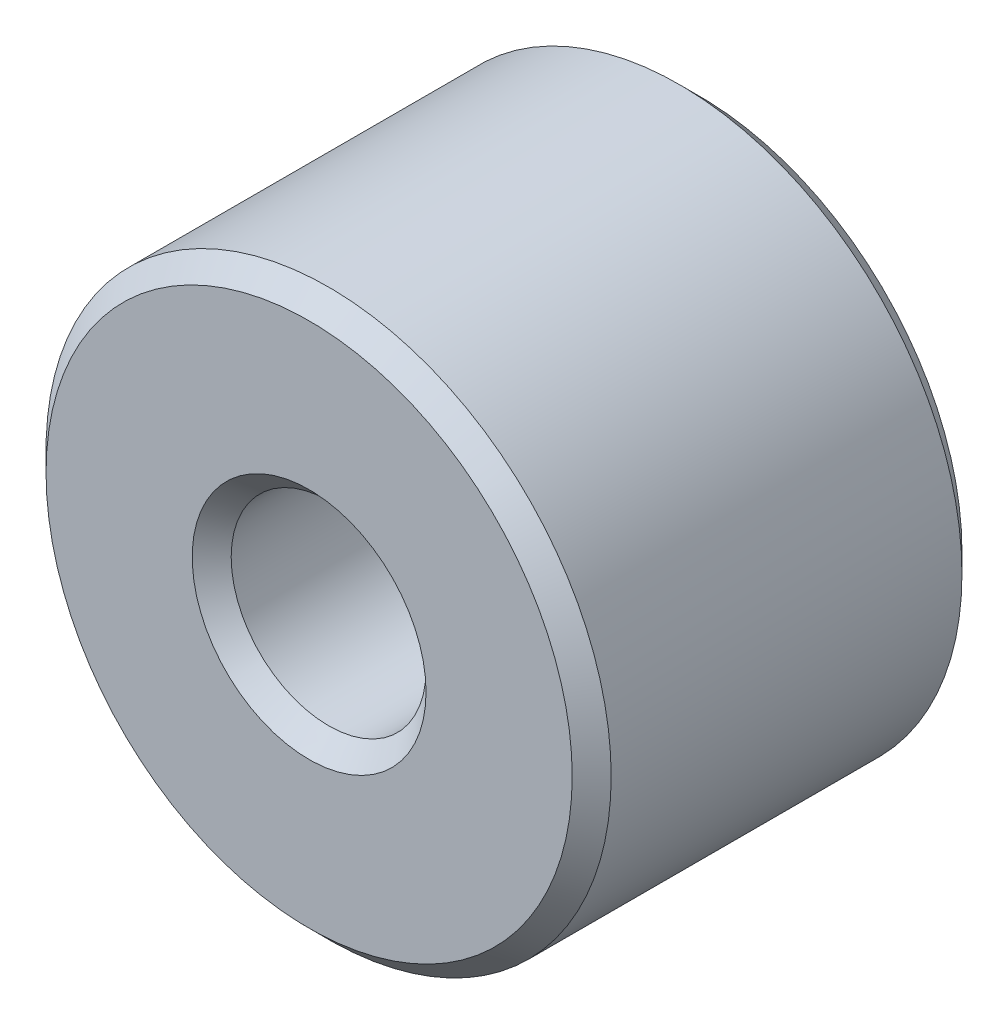
SolidWorks part; units mm, degrees
material "Plain Carbon Steel"
ref_plane "Front Plane" through (0, 0, 0) normal (0, 0, 1) x (1, 0, 0)
ref_plane "Top Plane" through (0, 0, 0) normal (0, 1, 0) x (1, 0, 0)
ref_plane "Right Plane" through (0, 0, 0) normal (1, 0, 0) x (0, 0, -1)
sketch "Sketch1" plane through (0, 0, 0) normal (0, 0, 1) x (1, 0, 0)
  circle A0 centre (0, 0) radius 7.25
  circle A1 centre (0, 0) radius 2.5
  dimension "D1" = 5
  dimension "D2" = 14.5
extrude "Boss-Extrude1" add sketch "Sketch1" along normal blind 10
chamfer "Chamfer1" distance 0.5 angle 45 4 edges at (2.5, 0, 0) (7.25, 0, 0) (2.5, 0, 10) (7.25, 0, 10)
